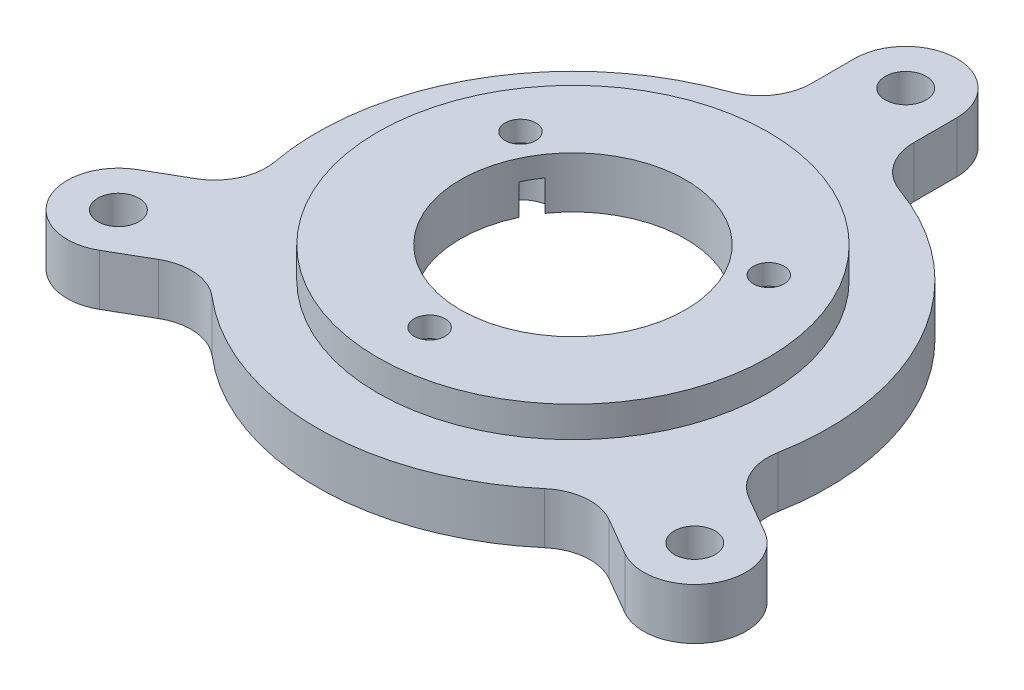
SolidWorks part; units mm, degrees
ref_plane "Front Plane" through (0, 0, 0) normal (0, 0, 1) x (1, 0, 0)
ref_plane "Top Plane" through (0, 0, 0) normal (0, 1, 0) x (1, 0, 0)
ref_plane "Right Plane" through (0, 0, 0) normal (1, 0, 0) x (0, 0, -1)
sketch "Sketch1" plane through (0, 0, 0) normal (0, 1, 0) x (1, 0, 0)
  line L0 (0, 32.5) -> (0, 0) construction
  line L1 (0, 0) -> (-28.1458, -16.25) construction
  line L2 (30.6458, -11.9199) -> (26.9949, -9.812)
  line L3 (28.1458, -16.25) -> (0, 0) construction
  line L4 (5, 32.5) -> (5, 28.2843)
  line L5 (-5, 32.5) -> (-5, 28.2843)
  line L6 (25.6458, -20.5801) -> (21.9949, -18.4723)
  line L7 (-25.6458, -20.5801) -> (-21.9949, -18.4723)
  line L8 (-30.6458, -11.9199) -> (-26.9949, -9.812)
  circle A0 centre (0, 0) radius 16
  circle A1 centre (0, 0) radius 32.5 construction
  circle A2 centre (0, 32.5) radius 2
  circle A3 centre (-28.1458, -16.25) radius 2
  circle A4 centre (28.1458, -16.25) radius 2
  arc A5 (-8.3333, 23.5702) -> (-24.5791, -4.5682) centre (0, 0) ccw
  arc A6 (-5, 32.5) -> (5, 32.5) centre (0, 32.5) cw
  arc A7 (30.6458, -11.9199) -> (25.6458, -20.5801) centre (28.1458, -16.25) cw
  arc A8 (-25.6458, -20.5801) -> (-30.6458, -11.9199) centre (-28.1458, -16.25) cw
  arc A9 (-16.2457, -19.002) -> (16.2457, -19.002) centre (0, 0) ccw
  arc A10 (24.5791, -4.5682) -> (8.3333, 23.5702) centre (0, 0) ccw
  arc A11 (-26.9949, -9.812) -> (-24.5791, -4.5682) centre (-29.4949, -5.4819) ccw
  arc A12 (-21.9949, -18.4723) -> (-16.2457, -19.002) centre (-19.4949, -22.8024) cw
  arc A13 (21.9949, -18.4723) -> (16.2457, -19.002) centre (19.4949, -22.8024) ccw
  arc A14 (26.9949, -9.812) -> (24.5791, -4.5682) centre (29.4949, -5.4819) cw
  arc A15 (5, 28.2843) -> (8.3333, 23.5702) centre (10, 28.2843) ccw
  arc A16 (-5, 28.2843) -> (-8.3333, 23.5702) centre (-10, 28.2843) cw
  point P27 (0, 0)
  dimension "D1" = 32
  dimension "D2" = 120
  dimension "D4" = 4
  dimension "D5" = 5
  dimension "D6" = 25
  dimension "D7" = 65
  dimension "D9" = 5
  dimension "D3" = 120
  dimension "D8" = 3
extrude "Boss-Extrude1" add sketch "Sketch1" along normal blind 8
sketch "Sketch4" plane through (0, 8, 0) normal (0, 1, 0) x (1, 0, 0)
  circle A0 centre (0, 0) radius 11
  circle A1 centre (0, 0) radius 16
  dimension "D1" = 22
extrude "Boss-Extrude3" add sketch "Sketch4" against normal blind 5
sketch "Sketch5" plane through (0, 8, 0) normal (0, 1, 0) x (1, 0, 0)
  line L0 (0, 0) -> (0, -14) construction
  circle A0 centre (0, -14) radius 1.5
  circle A1 centre (-12.1244, 7) radius 1.5
  circle A2 centre (12.1244, 7) radius 1.5
  point P11 (0, 0)
  dimension "D1" = 3
  dimension "D2" = 14
  dimension "D3" = 3
extrude "Cut-Extrude2" cut sketch "Sketch5" against normal through all
sketch "Sketch6" plane through (0, 0, 0) normal (0, -1, 0) x (1, 0, 0)
  circle A0 centre (0, 14) radius 3.175
  circle A1 centre (-12.1244, -7) radius 3.175
  circle A2 centre (12.1244, -7) radius 3.175
  dimension "D1" = 6.35
extrude "Cut-Extrude3" cut sketch "Sketch6" against normal offset from surface (6 mm away) 3 up to face at (12.1244, 3, -5.5) offset beyond the face yes
sketch "Sketch7" plane through (0, 8, 0) normal (0, 1, 0) x (1, 0, 0)
  circle A0 centre (0, 0) radius 19.075
  dimension "D1" = 38.15
extrude "Cut-Extrude4" cut sketch "Sketch7" against normal blind 3 flip side to cut
